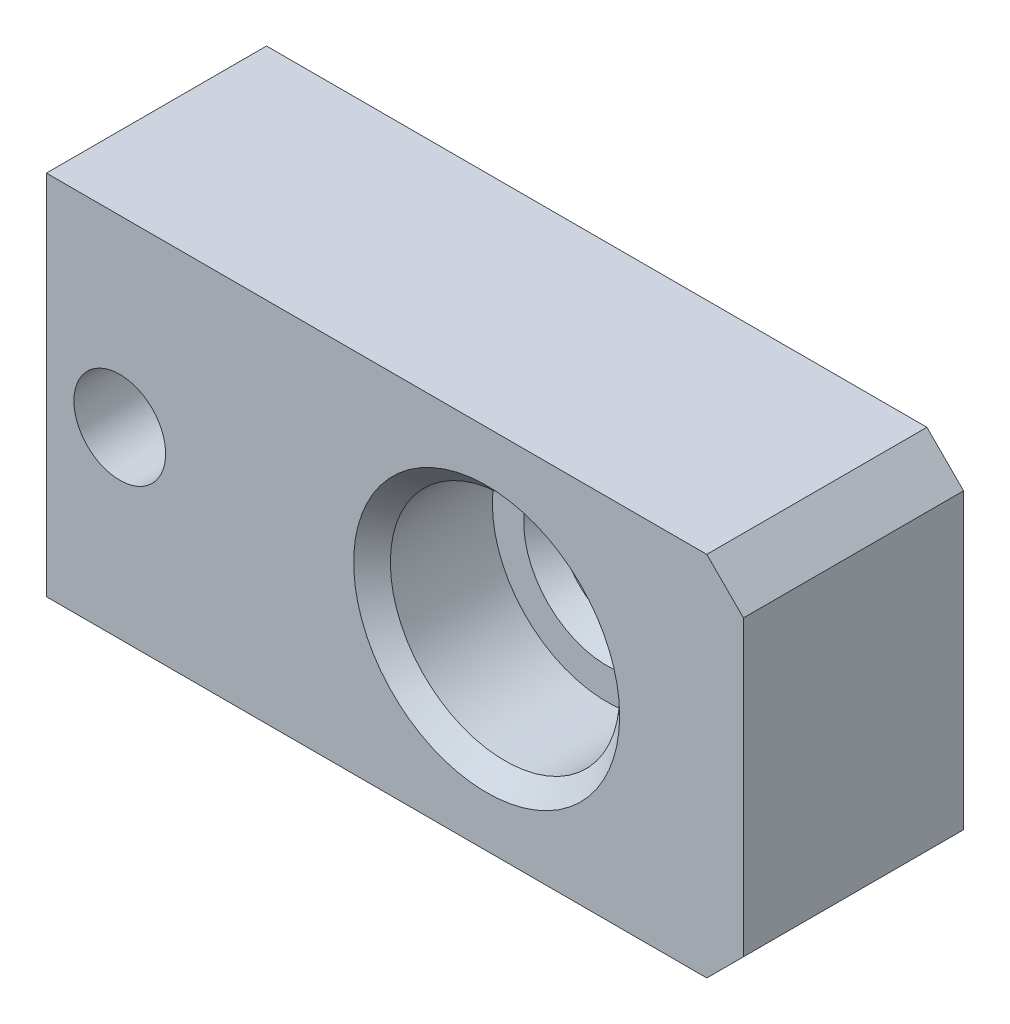
SolidWorks part; units mm, degrees
material "6061-T6 Al"
ref_plane "Front" through (0, 0, 0) normal (0, 0, 1) x (1, 0, 0)
ref_plane "Top" through (0, 0, 0) normal (0, 1, 0) x (1, 0, 0)
ref_plane "Right" through (0, 0, 0) normal (1, 0, 0) x (0, 0, -1)
sketch "Sketch1" plane through (0, 0, 0) normal (0, 0, 1) x (1, 0, 0)
  line L0 (0, 6.35) -> (25.4, 6.35) construction
  line L1 (0, 0) -> (25.4, 0)
  line L2 (0, 0) -> (0, 12.7)
  line L3 (0, 12.7) -> (25.4, 12.7)
  line L4 (25.4, 0) -> (25.4, 12.7)
  circle A1 centre (16.51, 6.35) radius 1.27
  dimension "D3" = 16.51
  dimension "D6" = 2.54
  dimension "D1" = 25.4
  dimension "D2" = 12.7
extrude "Extrude1" add sketch "Sketch1" along normal blind 7.62
chamfer "Chamfer1" distance 1.27 angle 45 6 edges at (0, 6.35, 0) (0, 6.35, 7.62) (25.4, 12.7, 3.81) (25.4, 0, 3.81) (0, 12.7, 3.81) (0, 0, 3.81)
hole_wizard "CBORE for #8 Socket Head Cap Screw1" positions "Sketch3" profile "Sketch2" counterbore size "#8" standard "Ansi Inch" end condition through all
sketch "Sketch3" plane through (4.0423, -0.4952, 7.62) normal (0, 0, -1) x (-1, 0, 0)
  point P0 (-12.4677, 6.8452)
sketch "Sketch2" plane through (16.51, 6.35, 7.62) normal (1, 0, 0) x (0, -1, 0)
  line L0 (0, 0) -> (0, 7.62)
  line L1 (2.2479, 6.985) -> (2.8829, 7.62)
  line L2 (2.2479, 6.985) -> (2.2479, 4.8006)
  line L3 (2.2479, 4.8006) -> (2.8829, 4.1656)
  line L4 (2.8829, 4.1656) -> (3.9687, 4.1656)
  line L5 (3.9687, 4.1656) -> (3.9687, 0.635)
  line L6 (3.9687, 0.635) -> (4.6037, 0)
  line L7 (4.6037, 0) -> (0, 0)
  line L8 (-3.9687, 0.635) -> (-4.6037, 0) construction
  line L9 (-2.2479, 4.8006) -> (-2.8829, 4.1656) construction
  line L11 (0, -6.35) -> (0, 107.95) construction
  line L12 (2.8829, 7.62) -> (0, 7.62)
  line L13 (-2.2479, 6.985) -> (-2.8829, 7.62) construction
  dimension "Thru Hole Dia." = 4.4958
  dimension "Thru Hole Depth" = 7.62
  dimension "C'Bore Dia." = 7.9375
  dimension "C'Bore Depth" = 4.1656
  dimension "Near C'Sink Dia." = 9.2075
  dimension "Near C'Sink Angle" = 90
  dimension "Mid C'Sink Dia." = 5.7658
  dimension "Mid C'Sink Angle" = 90
  dimension "Far C'Sink Dia." = 5.7658
  dimension "Far C'Sink Angle" = 90
hole_wizard "CBORE for #4 Socket Head Cap Screw1" positions "Sketch5" profile "Sketch4" counterbore size "#4" standard "Ansi Inch" end condition through all
sketch "Sketch5" plane through (0, 0, 0) normal (0, 0, -1) x (-1, 0, 0)
  line L0 (-16.51, 6.35) -> (-3.81, 6.35) construction
  point P0 (-3.81, 6.35)
  dimension "D1" = 12.7
sketch "Sketch4" plane through (3.81, 6.35, 0) normal (1, 0, 0) x (0, 1, 0)
  line L0 (0, 0) -> (0, 7.62)
  line L1 (0, 7.62) -> (1.5875, 7.62)
  line L3 (1.5875, 7.62) -> (1.5875, 1.524)
  line L4 (1.6002, 1.524) -> (1.5875, 1.524)
  line L5 (1.6002, 1.524) -> (1.6002, 0.3048)
  line L6 (1.6002, 0.3048) -> (1.905, 0)
  line L7 (1.905, 0) -> (0, 0)
  line L8 (-1.6002, 0.3048) -> (-1.905, 0) construction
  line L11 (0, -6.35) -> (0, 107.95) construction
  dimension "Thru Hole Dia." = 3.175
  dimension "Thru Hole Depth" = 7.62
  dimension "C'Bore Dia." = 3.2004
  dimension "C'Bore Depth" = 1.524
  dimension "Near C'Sink Dia." = 3.81
  dimension "Near C'Sink Angle" = 90
